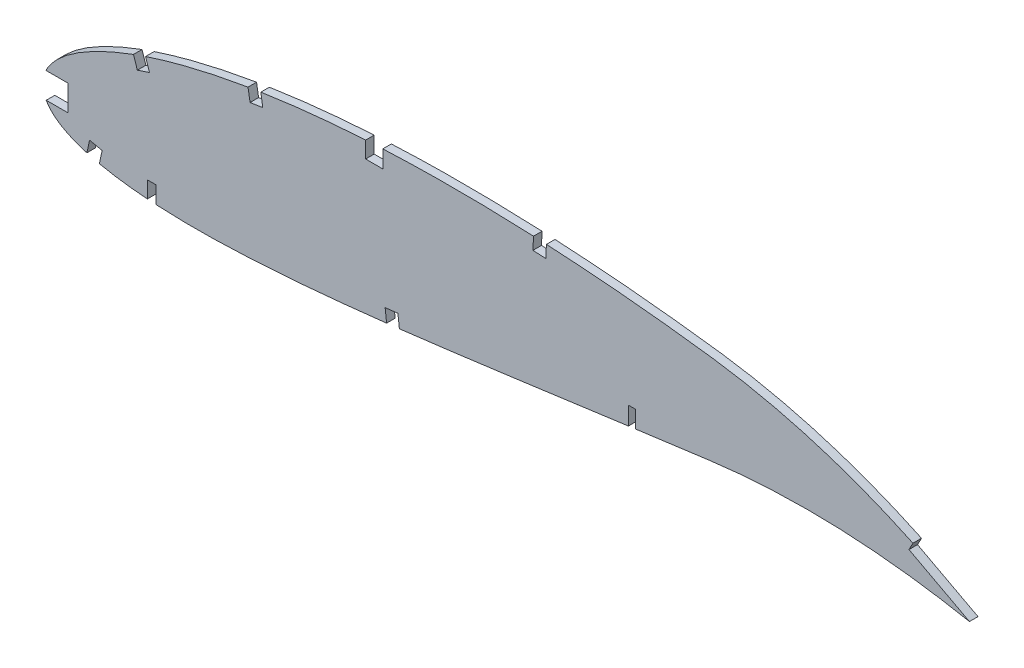
SolidWorks part; units mm, degrees
material "Plywood"
ref_plane "Front Plane" through (0, 0, 0) normal (0, 0, 1) x (1, 0, 0)
ref_plane "Top Plane" through (0, 0, 0) normal (0, 1, 0) x (1, 0, 0)
ref_plane "Right Plane" through (0, 0, 0) normal (1, 0, 0) x (0, 0, -1)
curve "Curve4"
  spline degree 3 poles (349.8746, 0.5455, 0) (349.8478, 0.562, 0) (349.7407, 0.6282, 0) (349.4993, 0.7762, 0) (349.0975, 1.0228, 0) (348.5349, 1.3661, 0) (347.8121, 1.8054, 0) (346.9286, 2.3375, 0) (345.885, 2.9606, 0) (344.6816, 3.6719, 0) (343.3185, 4.4681, 0) (341.7962, 5.3458, 0) (340.1148, 6.3001, 0) (338.275, 7.3272, 0) (336.2775, 8.422, 0) (334.1225, 9.5798, 0) (331.8109, 10.7946, 0) (329.3436, 12.0612, 0) (326.721, 13.3725, 0) (323.9443, 14.7232, 0) (321.0145, 16.1064, 0) (317.9326, 17.5149, 0) (314.7004, 18.9428, 0) (311.3186, 20.3813, 0) (307.7893, 21.8242, 0) (304.114, 23.2633, 0) (300.2949, 24.6919, 0) (296.3333, 26.1008, 0) (292.2323, 27.484, 0) (287.9939, 28.8323, 0) (283.6211, 30.1385, 0) (279.1164, 31.3942, 0) (274.4837, 32.5927, 0) (269.7257, 33.7256, 0) (264.8466, 34.785, 0) (259.8503, 35.7648, 0) (254.7409, 36.655, 0) (249.5326, 37.455, 0) (244.3091, 38.1205, 0) (239.0964, 38.7732, 0) (233.8915, 39.3864, 0) (228.623, 39.9736, 0) (223.2959, 40.5315, 0) (217.9156, 41.0583, 0) (212.4874, 41.5519, 0) (207.0171, 42.0107, 0) (201.5099, 42.4322, 0) (195.9716, 42.8157, 0) (190.4077, 43.1578, 0) (184.8241, 43.4583, 0) (179.2266, 43.7151, 0) (173.6208, 43.9264, 0) (168.0128, 44.0909, 0) (162.4085, 44.2071, 0) (156.8137, 44.2742, 0) (151.2345, 44.2904, 0) (145.6768, 44.2555, 0) (140.1465, 44.1681, 0) (134.6496, 44.0271, 0) (129.192, 43.8323, 0) (123.7796, 43.5837, 0) (118.4182, 43.2792, 0) (113.1138, 42.9209, 0) (107.8721, 42.5071, 0) (102.6991, 42.0378, 0) (97.6, 41.5149, 0) (92.5806, 40.937, 0) (87.6463, 40.3058, 0) (82.8024, 39.6225, 0) (78.0545, 38.8867, 0) (73.4074, 38.1005, 0) (68.8664, 37.2648, 0) (64.4362, 36.3819, 0) (60.1215, 35.4522, 0) (55.9271, 34.4784, 0) (51.8572, 33.4622, 0) (47.9162, 32.4055, 0) (44.1081, 31.3108, 0) (40.4368, 30.1806, 0) (36.9066, 29.0161, 0) (33.52, 27.8218, 0) (30.2813, 26.5985, 0) (27.193, 25.3499, 0) (24.2586, 24.0778, 0) (21.4804, 22.7861, 0) (18.8615, 21.4761, 0) (16.4038, 20.1517, 0) (14.1097, 18.8148, 0) (11.9815, 17.4679, 0) (10.02, 16.1143, 0) (8.2279, 14.7551, 0) (6.606, 13.3936, 0) (5.1551, 12.0318, 0) (3.8773, 10.6708, 0) (2.7727, 9.3129, 0) (1.8427, 7.9591, 0) (1.0874, 6.6108, 0) (0.5085, 5.269, 0) (0.1055, 3.9344, 0) (-0.1151, 2.6089, 0) (-0.17, 1.2916, 0) (-0.0566, 0.4299, 0) (0, 0, 0) knots 0 0 0 0 0.000254 0.001015 0.002283 0.004057 0.006331 0.009105 0.012374 0.016134 0.02038 0.025106 0.030306 0.035972 0.0421 0.048678 0.055702 0.06316 0.071046 0.07935 0.088063 0.097176 0.106678 0.116562 0.126814 0.137428 0.148394 0.1597 0.171338 0.183298 0.19557 0.208144 0.221012 0.234162 0.247587 0.261277 0.275223 0.289414 0.303771 0.317689 0.331784 0.34604 0.360444 0.374983 0.38964 0.404403 0.419257 0.434187 0.449177 0.464215 0.479284 0.49437 0.509458 0.524532 0.539579 0.554583 0.56953 0.584403 0.599191 0.613877 0.628447 0.642889 0.657186 0.671326 0.685294 0.699078 0.712665 0.726043 0.739198 0.752118 0.764792 0.777208 0.789356 0.801224 0.812804 0.824083 0.835055 0.84571 0.856038 0.866034 0.875689 0.884998 0.893953 0.902553 0.910789 0.918661 0.926166 0.933303 0.940071 0.946475 0.952518 0.958205 0.963547 0.968557 0.97325 0.977651 0.981787 0.985694 0.989415 0.993001 0.996508 1 1 1 1
curve "Curve5"
  spline degree 3 poles (0, 0, 0) (0.0898, -0.4241, 0) (0.27, -1.2744, 0) (0.7593, -2.4983, 0) (1.4064, -3.6749, 0) (2.2249, -4.801, 0) (3.2093, -5.8763, 0) (4.3574, -6.9018, 0) (5.6682, -7.8772, 0) (7.1398, -8.8018, 0) (8.7703, -9.6767, 0) (10.5577, -10.5014, 0) (12.5004, -11.2756, 0) (14.5962, -11.9982, 0) (16.8428, -12.6703, 0) (19.2378, -13.2904, 0) (21.7785, -13.8593, 0) (24.4626, -14.3755, 0) (27.2871, -14.8396, 0) (30.2491, -15.2513, 0) (33.3455, -15.6108, 0) (36.5732, -15.9174, 0) (39.9292, -16.1718, 0) (43.41, -16.3741, 0) (47.0123, -16.5249, 0) (50.7326, -16.6238, 0) (54.5673, -16.6722, 0) (58.5129, -16.6709, 0) (62.5656, -16.6195, 0) (66.7219, -16.5208, 0) (70.9777, -16.3742, 0) (75.3293, -16.1816, 0) (79.7728, -15.9448, 0) (84.3041, -15.6646, 0) (88.9192, -15.3423, 0) (93.6142, -14.9805, 0) (98.3848, -14.58, 0) (103.2269, -14.1432, 0) (108.136, -13.6724, 0) (113.1081, -13.1689, 0) (118.1387, -12.6351, 0) (123.2233, -12.0729, 0) (128.3576, -11.4851, 0) (133.537, -10.8728, 0) (138.7569, -10.2396, 0) (144.0126, -9.5866, 0) (149.2997, -8.9164, 0) (154.6133, -8.2321, 0) (159.9485, -7.5337, 0) (165.3008, -6.826, 0) (170.6651, -6.1086, 0) (176.0366, -5.3852, 0) (181.4105, -4.6578, 0) (186.7814, -3.9269, 0) (192.1447, -3.1954, 0) (197.4954, -2.4653, 0) (202.8282, -1.7368, 0) (208.1384, -1.0133, 0) (213.4205, -0.2949, 0) (218.6696, 0.417, 0) (223.8809, 1.1204, 0) (229.0493, 1.8142, 0) (234.1695, 2.4981, 0) (239.2364, 3.1723, 0) (244.169, 3.8163, 0) (248.9545, 4.4645, 0) (253.6088, 4.9959, 0) (258.2053, 5.4495, 0) (262.7485, 5.8213, 0) (267.2331, 6.1168, 0) (271.654, 6.3381, 0) (276.0058, 6.4882, 0) (280.283, 6.5716, 0) (284.4804, 6.5904, 0) (288.5922, 6.5507, 0) (292.613, 6.4555, 0) (296.5372, 6.3093, 0) (300.3594, 6.1169, 0) (304.0742, 5.8836, 0) (307.6759, 5.6128, 0) (311.1595, 5.3108, 0) (314.5196, 4.9821, 0) (317.7512, 4.6304, 0) (320.8494, 4.263, 0) (323.8094, 3.8825, 0) (326.6267, 3.4951, 0) (329.2966, 3.1046, 0) (331.8151, 2.7161, 0) (334.1781, 2.3332, 0) (336.3819, 1.9612, 0) (338.423, 1.6033, 0) (340.2977, 1.2632, 0) (342.0037, 0.9451, 0) (343.5374, 0.6506, 0) (344.8968, 0.3845, 0) (346.0794, 0.1481, 0) (347.0834, -0.0554, 0) (347.9072, -0.2251, 0) (348.5494, -0.3583, 0) (349.0088, -0.4551, 0) (349.2849, -0.5128, 0) (349.4076, -0.5389, 0) (349.4382, -0.5455, 0) knots 0 0 0 0 0.003638 0.007293 0.011028 0.014901 0.018963 0.023258 0.027821 0.032679 0.037853 0.043362 0.049215 0.055422 0.061989 0.068918 0.076211 0.083868 0.091887 0.100266 0.109 0.118085 0.127515 0.137285 0.147388 0.157816 0.168563 0.179619 0.190977 0.202627 0.21456 0.226767 0.239236 0.251959 0.264924 0.27812 0.291536 0.30516 0.318981 0.332985 0.347163 0.361499 0.375981 0.390597 0.405333 0.420175 0.43511 0.450124 0.465203 0.480333 0.495501 0.51069 0.525887 0.541078 0.556247 0.571382 0.586466 0.601485 0.616424 0.631269 0.646007 0.660621 0.675098 0.689423 0.703582 0.716908 0.730009 0.742952 0.755726 0.76832 0.780724 0.792927 0.804916 0.816679 0.828204 0.839475 0.850481 0.861208 0.871639 0.881763 0.891564 0.901027 0.910139 0.918884 0.927249 0.935221 0.942785 0.949928 0.956638 0.962904 0.968712 0.974054 0.978918 0.983297 0.98718 0.990561 0.993433 0.995791 0.99763 0.998946 0.999737 1 1 1 1
sketch "Sketch1" plane through (0, 0, 0) normal (0, 0, 1) x (1, 0, 0)
  line L24 (349.8746, 0.5455) -> (352.7074, -1.2046)
  line L25 (349.4382, -0.5455) -> (352.7074, -1.2046)
  spline S1 degree 3 poles (-6751.1592, -1841.0295) (107.2346, 81.5981) (-8.9881, 21.883) (0.7593, -2.4983) (1.4064, -3.6749) (2.2249, -4.801) (3.2093, -5.8763) (4.3574, -6.9018) (5.6682, -7.8772) (7.1398, -8.8018) (8.7703, -9.6767) (10.5577, -10.5014) (12.5004, -11.2756) (14.5962, -11.9982) (16.8428, -12.6703) (19.2378, -13.2904) (21.7785, -13.8593) (24.4626, -14.3755) (27.2871, -14.8396) (30.2491, -15.2513) (33.3455, -15.6108) (36.5732, -15.9174) (39.9292, -16.1718) (43.41, -16.3741) (47.0123, -16.5249) (50.7326, -16.6238) (54.5673, -16.6722) (58.5129, -16.6709) (62.5656, -16.6195) (66.7219, -16.5208) (70.9777, -16.3742) (75.3293, -16.1816) (79.7728, -15.9448) (84.3041, -15.6646) (88.9192, -15.3423) (93.6142, -14.9805) (98.3848, -14.58) (103.2269, -14.1432) (108.136, -13.6724) (113.1081, -13.1689) (118.1387, -12.6351) (123.2233, -12.0729) (128.3576, -11.4851) (133.537, -10.8728) (138.7569, -10.2396) (144.0126, -9.5866) (149.2997, -8.9164) (154.6133, -8.2321) (159.9485, -7.5337) (165.3008, -6.826) (170.6651, -6.1086) (176.0366, -5.3852) (181.4105, -4.6578) (186.7814, -3.9269) (192.1447, -3.1954) (197.4954, -2.4653) (202.8282, -1.7368) (208.1384, -1.0133) (213.4205, -0.2949) (218.6696, 0.417) (223.8809, 1.1204) (229.0493, 1.8142) (234.1695, 2.4981) (239.2364, 3.1723) (244.169, 3.8163) (248.9545, 4.4645) (253.6088, 4.9959) (258.2053, 5.4495) (262.7485, 5.8213) (267.2331, 6.1168) (271.654, 6.3381) (276.0058, 6.4882) (280.283, 6.5716) (284.4804, 6.5904) (288.5922, 6.5507) (292.613, 6.4555) (296.5372, 6.3093) (300.3594, 6.1169) (304.0742, 5.8836) (307.6759, 5.6128) (311.1595, 5.3108) (314.5196, 4.9821) (317.7512, 4.6304) (320.8494, 4.263) (323.8094, 3.8825) (326.6267, 3.4951) (329.2966, 3.1046) (331.8151, 2.7161) (334.1781, 2.3332) (336.3819, 1.9612) (338.423, 1.6033) (340.2977, 1.2632) (342.0037, 0.9451) (343.5374, 0.6506) (344.8968, 0.3845) (346.0794, 0.1481) (347.0834, -0.0554) (347.9072, -0.2251) (348.5494, -0.3583) (349.0088, -0.4551) (367.3245, -4.278) (382.9912, -19.8695) (1851.2191, 6833.2949) knots -0.208652 -0.208652 -0.208652 -0.208652 0.003638 0.007293 0.011028 0.014901 0.018963 0.023258 0.027821 0.032679 0.037853 0.043362 0.049215 0.055422 0.061989 0.068918 0.076211 0.083868 0.091887 0.100266 0.109 0.118085 0.127515 0.137285 0.147388 0.157816 0.168563 0.179619 0.190977 0.202627 0.21456 0.226767 0.239236 0.251959 0.264924 0.27812 0.291536 0.30516 0.318981 0.332985 0.347163 0.361499 0.375981 0.390597 0.405333 0.420175 0.43511 0.450124 0.465203 0.480333 0.495501 0.51069 0.525887 0.541078 0.556247 0.571382 0.586466 0.601485 0.616424 0.631269 0.646007 0.660621 0.675098 0.689423 0.703582 0.716908 0.730009 0.742952 0.755726 0.76832 0.780724 0.792927 0.804916 0.816679 0.828204 0.839475 0.850481 0.861208 0.871639 0.881763 0.891564 0.901027 0.910139 0.918884 0.927249 0.935221 0.942785 0.949928 0.956638 0.962904 0.968712 0.974054 0.978918 0.983297 0.98718 0.990561 0.993433 0.995791 0.99763 0.998946 0.999737 1.154885 1.154885 1.154885 1.154885 only from (0, 0) to (349.4382, -0.5455) construction
  spline S3 degree 3 poles (4072.2429, 5924.9131) (379.309, -30.208) (367.3101, -10.1487) (349.4993, 0.7762) (349.0975, 1.0228) (348.5349, 1.3661) (347.8121, 1.8054) (346.9286, 2.3375) (345.885, 2.9606) (344.6816, 3.6719) (343.3185, 4.4681) (341.7962, 5.3458) (340.1148, 6.3001) (338.275, 7.3272) (336.2775, 8.422) (334.1225, 9.5798) (331.8109, 10.7946) (329.3436, 12.0612) (326.721, 13.3725) (323.9443, 14.7232) (321.0145, 16.1064) (317.9326, 17.5149) (314.7004, 18.9428) (311.3186, 20.3813) (307.7893, 21.8242) (304.114, 23.2633) (300.2949, 24.6919) (296.3333, 26.1008) (292.2323, 27.484) (287.9939, 28.8323) (283.6211, 30.1385) (279.1164, 31.3942) (274.4837, 32.5927) (269.7257, 33.7256) (264.8466, 34.785) (259.8503, 35.7648) (254.7409, 36.655) (249.5326, 37.455) (244.3091, 38.1205) (239.0964, 38.7732) (233.8915, 39.3864) (228.623, 39.9736) (223.2959, 40.5315) (217.9156, 41.0583) (212.4874, 41.5519) (207.0171, 42.0107) (201.5099, 42.4322) (195.9716, 42.8157) (190.4077, 43.1578) (184.8241, 43.4583) (179.2266, 43.7151) (173.6208, 43.9264) (168.0128, 44.0909) (162.4085, 44.2071) (156.8137, 44.2742) (151.2345, 44.2904) (145.6768, 44.2555) (140.1465, 44.1681) (134.6496, 44.0271) (129.192, 43.8323) (123.7796, 43.5837) (118.4182, 43.2792) (113.1138, 42.9209) (107.8721, 42.5071) (102.6991, 42.0378) (97.6, 41.5149) (92.5806, 40.937) (87.6463, 40.3058) (82.8024, 39.6225) (78.0545, 38.8867) (73.4074, 38.1005) (68.8664, 37.2648) (64.4362, 36.3819) (60.1215, 35.4522) (55.9271, 34.4784) (51.8572, 33.4622) (47.9162, 32.4055) (44.1081, 31.3108) (40.4368, 30.1806) (36.9066, 29.0161) (33.52, 27.8218) (30.2813, 26.5985) (27.193, 25.3499) (24.2586, 24.0778) (21.4804, 22.7861) (18.8615, 21.4761) (16.4038, 20.1517) (14.1097, 18.8148) (11.9815, 17.4679) (10.02, 16.1143) (8.2279, 14.7551) (6.606, 13.3936) (5.1551, 12.0318) (3.8773, 10.6708) (2.7727, 9.3129) (1.8427, 7.9591) (1.0874, 6.6108) (0.5085, 5.269) (0.1055, 3.9344) (-0.1151, 2.6089) (-1.2068, -23.58) (128.5217, -41.162) (-6978.7548, -509.825) knots -0.166234 -0.166234 -0.166234 -0.166234 0.000254 0.001015 0.002283 0.004057 0.006331 0.009105 0.012374 0.016134 0.02038 0.025106 0.030306 0.035972 0.0421 0.048678 0.055702 0.06316 0.071046 0.07935 0.088063 0.097176 0.106678 0.116562 0.126814 0.137428 0.148394 0.1597 0.171338 0.183298 0.19557 0.208144 0.221012 0.234162 0.247587 0.261277 0.275223 0.289414 0.303771 0.317689 0.331784 0.34604 0.360444 0.374983 0.38964 0.404403 0.419257 0.434187 0.449177 0.464215 0.479284 0.49437 0.509458 0.524532 0.539579 0.554583 0.56953 0.584403 0.599191 0.613877 0.628447 0.642889 0.657186 0.671326 0.685294 0.699078 0.712665 0.726043 0.739198 0.752118 0.764792 0.777208 0.789356 0.801224 0.812804 0.824083 0.835055 0.84571 0.856038 0.866034 0.875689 0.884998 0.893953 0.902553 0.910789 0.918661 0.926166 0.933303 0.940071 0.946475 0.952518 0.958205 0.963547 0.968557 0.97325 0.977651 0.981787 0.985694 0.989415 0.993001 0.996508 1.199844 1.199844 1.199844 1.199844 only from (349.8746, 0.5455) to (0, 0) construction
  spline S4 degree 3 poles (0, 0) (0.0898, -0.4241) (0.27, -1.2744) (0.7593, -2.4983) (1.4064, -3.6749) (2.2249, -4.801) (3.2093, -5.8763) (4.3574, -6.9018) (5.6682, -7.8772) (7.1398, -8.8018) (8.7703, -9.6767) (10.5577, -10.5014) (12.5004, -11.2756) (14.5962, -11.9982) (16.8428, -12.6703) (19.2378, -13.2904) (21.7785, -13.8593) (24.4626, -14.3755) (27.2871, -14.8396) (30.2491, -15.2513) (33.3455, -15.6108) (36.5732, -15.9174) (39.9292, -16.1718) (43.41, -16.3741) (47.0123, -16.5249) (50.7326, -16.6238) (54.5673, -16.6722) (58.5129, -16.6709) (62.5656, -16.6195) (66.7219, -16.5208) (70.9777, -16.3742) (75.3293, -16.1816) (79.7728, -15.9448) (84.3041, -15.6646) (88.9192, -15.3423) (93.6142, -14.9805) (98.3848, -14.58) (103.2269, -14.1432) (108.136, -13.6724) (113.1081, -13.1689) (118.1387, -12.6351) (123.2233, -12.0729) (128.3576, -11.4851) (133.537, -10.8728) (138.7569, -10.2396) (144.0126, -9.5866) (149.2997, -8.9164) (154.6133, -8.2321) (159.9485, -7.5337) (165.3008, -6.826) (170.6651, -6.1086) (176.0366, -5.3852) (181.4105, -4.6578) (186.7814, -3.9269) (192.1447, -3.1954) (197.4954, -2.4653) (202.8282, -1.7368) (208.1384, -1.0133) (213.4205, -0.2949) (218.6696, 0.417) (223.8809, 1.1204) (229.0493, 1.8142) (234.1695, 2.4981) (239.2364, 3.1723) (244.169, 3.8163) (248.9545, 4.4645) (253.6088, 4.9959) (258.2053, 5.4495) (262.7485, 5.8213) (267.2331, 6.1168) (271.654, 6.3381) (276.0058, 6.4882) (280.283, 6.5716) (284.4804, 6.5904) (288.5922, 6.5507) (292.613, 6.4555) (296.5372, 6.3093) (300.3594, 6.1169) (304.0742, 5.8836) (307.6759, 5.6128) (311.1595, 5.3108) (314.5196, 4.9821) (317.7512, 4.6304) (320.8494, 4.263) (323.8094, 3.8825) (326.6267, 3.4951) (329.2966, 3.1046) (331.8151, 2.7161) (334.1781, 2.3332) (336.3819, 1.9612) (338.423, 1.6033) (340.2977, 1.2632) (342.0037, 0.9451) (343.5374, 0.6506) (344.8968, 0.3845) (346.0794, 0.1481) (347.0834, -0.0554) (347.9072, -0.2251) (348.5494, -0.3583) (349.0088, -0.4551) (349.2849, -0.5128) (349.4076, -0.5389) (349.4382, -0.5455) knots 0 0 0 0 0.003638 0.007293 0.011028 0.014901 0.018963 0.023258 0.027821 0.032679 0.037853 0.043362 0.049215 0.055422 0.061989 0.068918 0.076211 0.083868 0.091887 0.100266 0.109 0.118085 0.127515 0.137285 0.147388 0.157816 0.168563 0.179619 0.190977 0.202627 0.21456 0.226767 0.239236 0.251959 0.264924 0.27812 0.291536 0.30516 0.318981 0.332985 0.347163 0.361499 0.375981 0.390597 0.405333 0.420175 0.43511 0.450124 0.465203 0.480333 0.495501 0.51069 0.525887 0.541078 0.556247 0.571382 0.586466 0.601485 0.616424 0.631269 0.646007 0.660621 0.675098 0.689423 0.703582 0.716908 0.730009 0.742952 0.755726 0.76832 0.780724 0.792927 0.804916 0.816679 0.828204 0.839475 0.850481 0.861208 0.871639 0.881763 0.891564 0.901027 0.910139 0.918884 0.927249 0.935221 0.942785 0.949928 0.956638 0.962904 0.968712 0.974054 0.978918 0.983297 0.98718 0.990561 0.993433 0.995791 0.99763 0.998946 0.999737 1 1 1 1
  spline S5 degree 3 poles (349.8746, 0.5455) (349.8478, 0.562) (349.7407, 0.6282) (349.4993, 0.7762) (349.0975, 1.0228) (348.5349, 1.3661) (347.8121, 1.8054) (346.9286, 2.3375) (345.885, 2.9606) (344.6816, 3.6719) (343.3185, 4.4681) (341.7962, 5.3458) (340.1148, 6.3001) (338.275, 7.3272) (336.2775, 8.422) (334.1225, 9.5798) (331.8109, 10.7946) (329.3436, 12.0612) (326.721, 13.3725) (323.9443, 14.7232) (321.0145, 16.1064) (317.9326, 17.5149) (314.7004, 18.9428) (311.3186, 20.3813) (307.7893, 21.8242) (304.114, 23.2633) (300.2949, 24.6919) (296.3333, 26.1008) (292.2323, 27.484) (287.9939, 28.8323) (283.6211, 30.1385) (279.1164, 31.3942) (274.4837, 32.5927) (269.7257, 33.7256) (264.8466, 34.785) (259.8503, 35.7648) (254.7409, 36.655) (249.5326, 37.455) (244.3091, 38.1205) (239.0964, 38.7732) (233.8915, 39.3864) (228.623, 39.9736) (223.2959, 40.5315) (217.9156, 41.0583) (212.4874, 41.5519) (207.0171, 42.0107) (201.5099, 42.4322) (195.9716, 42.8157) (190.4077, 43.1578) (184.8241, 43.4583) (179.2266, 43.7151) (173.6208, 43.9264) (168.0128, 44.0909) (162.4085, 44.2071) (156.8137, 44.2742) (151.2345, 44.2904) (145.6768, 44.2555) (140.1465, 44.1681) (134.6496, 44.0271) (129.192, 43.8323) (123.7796, 43.5837) (118.4182, 43.2792) (113.1138, 42.9209) (107.8721, 42.5071) (102.6991, 42.0378) (97.6, 41.5149) (92.5806, 40.937) (87.6463, 40.3058) (82.8024, 39.6225) (78.0545, 38.8867) (73.4074, 38.1005) (68.8664, 37.2648) (64.4362, 36.3819) (60.1215, 35.4522) (55.9271, 34.4784) (51.8572, 33.4622) (47.9162, 32.4055) (44.1081, 31.3108) (40.4368, 30.1806) (36.9066, 29.0161) (33.52, 27.8218) (30.2813, 26.5985) (27.193, 25.3499) (24.2586, 24.0778) (21.4804, 22.7861) (18.8615, 21.4761) (16.4038, 20.1517) (14.1097, 18.8148) (11.9815, 17.4679) (10.02, 16.1143) (8.2279, 14.7551) (6.606, 13.3936) (5.1551, 12.0318) (3.8773, 10.6708) (2.7727, 9.3129) (1.8427, 7.9591) (1.0874, 6.6108) (0.5085, 5.269) (0.1055, 3.9344) (-0.1151, 2.6089) (-0.17, 1.2916) (-0.0566, 0.4299) (0, 0) knots 0 0 0 0 0.000254 0.001015 0.002283 0.004057 0.006331 0.009105 0.012374 0.016134 0.02038 0.025106 0.030306 0.035972 0.0421 0.048678 0.055702 0.06316 0.071046 0.07935 0.088063 0.097176 0.106678 0.116562 0.126814 0.137428 0.148394 0.1597 0.171338 0.183298 0.19557 0.208144 0.221012 0.234162 0.247587 0.261277 0.275223 0.289414 0.303771 0.317689 0.331784 0.34604 0.360444 0.374983 0.38964 0.404403 0.419257 0.434187 0.449177 0.464215 0.479284 0.49437 0.509458 0.524532 0.539579 0.554583 0.56953 0.584403 0.599191 0.613877 0.628447 0.642889 0.657186 0.671326 0.685294 0.699078 0.712665 0.726043 0.739198 0.752118 0.764792 0.777208 0.789356 0.801224 0.812804 0.824083 0.835055 0.84571 0.856038 0.866034 0.875689 0.884998 0.893953 0.902553 0.910789 0.918661 0.926166 0.933303 0.940071 0.946475 0.952518 0.958205 0.963547 0.968557 0.97325 0.977651 0.981787 0.985694 0.989415 0.993001 0.996508 1 1 1 1
extrude "Boss-Extrude1" add sketch "Sketch1" along normal blind 3.175
sketch "Sketch2" plane through (0, 0, 0) normal (0, 0, -1) x (-1, 0, 0)
  line L0 (-219.6066, 6.9148) -> (-217.0666, 6.9148)
  line L1 (-219.6066, 0.5647) -> (-219.6066, 6.9148)
  line L2 (-217.0666, 0.5647) -> (-217.0666, -0.7899)
  line L3 (-125.9441, 43.5934) -> (-125.9441, 37.241)
  line L4 (-217.0666, -0.7899) -> (-219.6066, -0.1126)
  line L5 (-41.8066, -16.2784) -> (-41.8066, -9.9284)
  line L6 (-219.6066, -0.1126) -> (-219.6066, 0.5647)
  line L7 (-38.6316, -16.2784) -> (-38.6316, -9.9284)
  line L8 (-125.9441, 37.241) -> (-119.5941, 37.241)
  line L9 (-119.5941, 43.5934) -> (-119.5941, 37.241)
  line L10 (-125.9441, 43.5934) -> (-125.9441, 46.4957)
  line L11 (-217.0666, 0.5647) -> (-217.0666, 6.9148)
  line L12 (-125.9441, 46.4957) -> (-119.5941, 44.8024)
  line L13 (-119.5941, 44.8024) -> (-119.5941, 43.5934)
  line L14 (-41.8066, -16.2784) -> (-38.6316, -16.2784)
  line L15 (-41.8066, -9.9284) -> (-38.6316, -9.9284)
extrude "Cut-Extrude1" cut sketch "Sketch2" against normal blind 7.62
sketch "Sketch3" plane through (0, 0, 3.175) normal (0, 0, 1) x (1, 0, 0)
  line L1 (-0.4071, 6.4083) -> (9.1179, 6.4083)
  line L2 (16.1715, -12.5452) -> (15.7059, -14.4019)
  line L3 (9.1179, -3.1167) -> (9.1179, 6.4083)
  line L4 (20.793, -13.704) -> (20.3275, -15.5607)
  line L5 (39.4213, 24.9477) -> (37.9149, 29.4655)
  line L6 (15.7059, -14.4019) -> (20.3275, -15.5607)
  line L7 (20.793, -13.704) -> (21.8392, -8.9067)
  line L9 (21.8392, -8.9067) -> (17.1861, -7.8921)
  line L10 (127.3683, -11.6175) -> (127.6344, -13.8855)
  line L11 (81.4236, 34.6803) -> (80.6994, 39.3875)
  line L12 (132.1136, -11.0609) -> (132.3796, -13.3289)
  line L13 (132.1136, -11.0609) -> (131.5505, -6.3243)
  line L14 (127.6344, -13.8855) -> (132.3796, -13.3289)
  line L15 (131.5505, -6.3243) -> (126.8213, -6.8865)
  line L17 (186.4034, 38.6915) -> (186.6522, 43.4474)
  line L19 (-0.4071, -3.1167) -> (-0.4071, 6.4083)
  line L21 (-0.4071, -3.1167) -> (9.1179, -3.1167)
  line L23 (33.4172, 27.8983) -> (34.9034, 23.4412)
  line L25 (34.9034, 23.4412) -> (39.4213, 24.9477)
  line L27 (17.1861, -7.8921) -> (16.1715, -12.5452)
  line L29 (75.932, 38.6201) -> (76.7164, 33.9561)
  line L31 (76.7164, 33.9561) -> (81.4236, 34.6803)
  line L33 (126.8213, -6.8865) -> (127.3683, -11.6175)
  line L35 (181.8631, 43.6817) -> (181.6474, 38.9402)
  line L37 (181.6474, 38.9402) -> (186.4034, 38.6915)
  arc A1 (186.6522, 43.4474) -> (181.8631, 43.6817) centre (149.7221, -662.3427) ccw
  spline S1 degree 3 poles (37.9149, 29.4655) (37.5031, 29.3282) (35.9987, 28.8207) (34.5011, 28.2932) (33.4172, 27.8983) knots 0 0 0 0 0.273428 1 1 1 1
  spline S3 degree 3 poles (80.6994, 39.3875) (79.7758, 39.2454) (78.1859, 38.9943) (76.5977, 38.7321) (75.932, 38.6201) knots 0 0 0 0 0.580571 1 1 1 1
extrude "Cut-Extrude2" cut sketch "Sketch3" against normal blind 7.62
sketch "Sketch4" plane through (0, 0, 3.175) normal (0, 0, 1) x (1, 0, 0)
  line L0 (322.6191, 15.347) -> (321.1318, 12.542)
  line L1 (322.6191, 15.347) -> (345.0596, 3.448)
  line L2 (321.1318, 12.542) -> (343.5722, 0.6429)
  line L3 (345.0596, 3.448) -> (343.5722, 0.6429)
  line L29 (1.0177, 6.4083) -> (9.1179, 6.4083)
  line L30 (9.1179, 6.4083) -> (9.1179, -3.1167)
  line L31 (9.1179, -3.1167) -> (1.1073, -3.1167)
  line L32 (16.1882, -12.4685) -> (17.1861, -7.8921)
  line L33 (17.1861, -7.8921) -> (21.8392, -8.9067)
  line L34 (21.8392, -8.9067) -> (20.8074, -13.6378)
  line L35 (38.6316, -16.0704) -> (38.6316, -9.9284)
  line L36 (38.6316, -9.9284) -> (41.8066, -9.9284)
  line L37 (41.8066, -9.9284) -> (41.8066, -16.2784)
  line L38 (127.366, -11.5969) -> (126.8213, -6.8865)
  line L39 (126.8213, -6.8865) -> (131.5505, -6.3243)
  line L40 (131.5505, -6.3243) -> (132.1111, -11.0403)
  line L41 (217.0666, 0.1994) -> (217.0666, 6.9148)
  line L42 (217.0666, 6.9148) -> (219.6066, 6.9148)
  line L43 (219.6066, 6.9148) -> (219.6066, 0.5432)
  line L44 (349.4382, -0.5455) -> (352.7074, -1.2046)
  line L45 (352.7074, -1.2046) -> (349.8746, 0.5455)
  line L46 (186.6475, 43.3577) -> (186.4034, 38.6915)
  line L47 (186.4034, 38.6915) -> (181.6474, 38.9402)
  line L48 (181.6474, 38.9402) -> (181.8591, 43.5924)
  line L49 (125.9441, 43.6804) -> (125.9441, 37.241)
  line L50 (125.9441, 37.241) -> (119.5941, 37.241)
  line L51 (119.5941, 37.241) -> (119.5941, 43.3413)
  line L52 (80.7135, 39.2958) -> (81.4236, 34.6803)
  line L53 (81.4236, 34.6803) -> (76.7164, 33.9561)
  line L54 (76.7164, 33.9561) -> (75.9476, 38.5273)
  line L55 (37.9515, 29.3559) -> (39.4213, 24.9477)
  line L56 (39.4213, 24.9477) -> (34.9034, 23.4412)
  line L57 (34.9034, 23.4412) -> (33.4552, 27.7843)
  line L58 (1.0177, 6.4083) -> (9.1179, 6.4083)
  line L59 (9.1179, 6.4083) -> (9.1179, -3.1167)
  line L60 (9.1179, -3.1167) -> (1.1073, -3.1167)
  line L61 (16.1882, -12.4685) -> (17.1861, -7.8921)
  line L62 (17.1861, -7.8921) -> (21.8392, -8.9067)
  line L63 (21.8392, -8.9067) -> (20.8074, -13.6378)
  line L64 (38.6316, -16.0704) -> (38.6316, -9.9284)
  line L65 (38.6316, -9.9284) -> (41.8066, -9.9284)
  line L66 (41.8066, -9.9284) -> (41.8066, -16.2784)
  line L67 (127.366, -11.5969) -> (126.8213, -6.8865)
  line L68 (126.8213, -6.8865) -> (131.5505, -6.3243)
  line L69 (131.5505, -6.3243) -> (132.1111, -11.0403)
  line L70 (217.0666, 0.1994) -> (217.0666, 6.9148)
  line L71 (217.0666, 6.9148) -> (219.6066, 6.9148)
  line L72 (219.6066, 6.9148) -> (219.6066, 0.5432)
  line L73 (349.4382, -0.5455) -> (352.7074, -1.2046)
  line L74 (352.7074, -1.2046) -> (349.8746, 0.5455)
  line L75 (186.6475, 43.3577) -> (186.4034, 38.6915)
  line L76 (186.4034, 38.6915) -> (181.6474, 38.9402)
  line L77 (181.6474, 38.9402) -> (181.8591, 43.5924)
  line L78 (125.9441, 43.6804) -> (125.9441, 37.241)
  line L79 (125.9441, 37.241) -> (119.5941, 37.241)
  line L80 (119.5941, 37.241) -> (119.5941, 43.3413)
  line L81 (80.7135, 39.2958) -> (81.4236, 34.6803)
  line L82 (81.4236, 34.6803) -> (76.7164, 33.9561)
  line L83 (76.7164, 33.9561) -> (75.9476, 38.5273)
  line L84 (37.9515, 29.3559) -> (39.4213, 24.9477)
  line L85 (39.4213, 24.9477) -> (34.9034, 23.4412)
  line L86 (34.9034, 23.4412) -> (33.4552, 27.7843)
  spline S10 degree 3 poles (-2134.0221, 3364.7605) (538.8254, -195.9198) (211.3259, 99.792) (27.193, 25.3499) (24.2586, 24.0778) (21.4804, 22.7861) (18.8615, 21.4761) (16.4038, 20.1517) (14.1097, 18.8148) (11.9815, 17.4679) (10.02, 16.1143) (8.2279, 14.7551) (6.606, 13.3936) (5.1551, 12.0318) (3.8773, 10.6708) (2.7727, 9.3129) (1.8427, 7.9591) (-20.1055, -31.2195) (140.4638, -160.6153) (3982.6931, 317.4313) knots -0.699136 -0.699136 -0.699136 -0.699136 0.884998 0.893953 0.902553 0.910789 0.918661 0.926166 0.933303 0.940071 0.946475 0.952518 0.958205 0.963547 0.968557 0.97325 0.977651 0.981787 1.334861 1.334861 1.334861 1.334861 only from (33.4552, 27.7843) to (1.0177, 6.4083)
  spline S11 degree 3 poles (2938.0839, -2689.8405) (246.7778, 269.8068) (-28.0545, 36.8583) (2.2249, -4.801) (3.2093, -5.8763) (4.3574, -6.9018) (5.6682, -7.8772) (7.1398, -8.8018) (8.7703, -9.6767) (10.5577, -10.5014) (12.5004, -11.2756) (106.4904, -43.6815) (280.4844, 176.1899) (-1938.6252, -3496.6913) knots -0.412769 -0.412769 -0.412769 -0.412769 0.011028 0.014901 0.018963 0.023258 0.027821 0.032679 0.037853 0.043362 0.049215 0.055422 0.878689 0.878689 0.878689 0.878689 only from (1.1073, -3.1167) to (16.1882, -12.4685)
  spline S12 degree 3 poles (1320.3281, 3756.9994) (-146.0598, 213.5353) (-80.6979, 5.8491) (24.4626, -14.3755) (27.2871, -14.8396) (30.2491, -15.2513) (33.3455, -15.6108) (213.0584, -32.6822) (415.285, 227.9801) (-474.0394, -3957.3928) knots -0.808032 -0.808032 -0.808032 -0.808032 0.076211 0.083868 0.091887 0.100266 0.109 0.118085 1.617405 1.617405 1.617405 1.617405 only from (20.8074, -13.6378) to (38.6316, -16.0704)
  spline S13 degree 3 poles (256.2221, 3952.659) (-280.3063, 190.6076) (-122.0561, -9.444) (47.0123, -16.5249) (50.7326, -16.6238) (54.5673, -16.6722) (58.5129, -16.6709) (62.5656, -16.6195) (66.7219, -16.5208) (70.9777, -16.3742) (75.3293, -16.1816) (79.7728, -15.9448) (84.3041, -15.6646) (88.9192, -15.3423) (93.6142, -14.9805) (98.3848, -14.58) (103.2269, -14.1432) (108.136, -13.6724) (113.1081, -13.1689) (118.1387, -12.6351) (616.9364, 42.523) (1082.5995, 376.7415) (1720.9864, -3408.5986) knots -1.264346 -1.264346 -1.264346 -1.264346 0.137285 0.147388 0.157816 0.168563 0.179619 0.190977 0.202627 0.21456 0.226767 0.239236 0.251959 0.264924 0.27812 0.291536 0.30516 0.318981 0.332985 0.347163 0.361499 4.550792 4.550792 4.550792 4.550792 only from (41.8066, -16.2784) to (127.366, -11.5969)
  spline S14 degree 3 poles (-1205.6276, 3667.8196) (-512.3075, 1.844) (-182.27, -49.1822) (138.7569, -10.2396) (144.0126, -9.5866) (149.2997, -8.9164) (154.6133, -8.2321) (159.9485, -7.5337) (165.3008, -6.826) (170.6651, -6.1086) (176.0366, -5.3852) (181.4105, -4.6578) (186.7814, -3.9269) (192.1447, -3.1954) (197.4954, -2.4653) (202.8282, -1.7368) (208.1384, -1.0133) (637.4453, 57.377) (1067.6455, 95.9352) (1973.8247, -3421.787) knots -2.297748 -2.297748 -2.297748 -2.297748 0.390597 0.405333 0.420175 0.43511 0.450124 0.465203 0.480333 0.495501 0.51069 0.525887 0.541078 0.556247 0.571382 0.586466 0.601485 0.616424 4.2279 4.2279 4.2279 4.2279 only from (132.1111, -11.0403) to (217.0666, 0.1994)
  spline S15 degree 3 poles (-2257.0625, 2699.4045) (-1158.0495, -286.0267) (-472.0862, -92.3082) (229.0493, 1.8142) (234.1695, 2.4981) (239.2364, 3.1723) (244.169, 3.8163) (248.9545, 4.4645) (253.6088, 4.9959) (258.2053, 5.4495) (262.7485, 5.8213) (267.2331, 6.1168) (271.654, 6.3381) (276.0058, 6.4882) (280.283, 6.5716) (284.4804, 6.5904) (288.5922, 6.5507) (292.613, 6.4555) (296.5372, 6.3093) (300.3594, 6.1169) (304.0742, 5.8836) (307.6759, 5.6128) (311.1595, 5.3108) (314.5196, 4.9821) (317.7512, 4.6304) (320.8494, 4.263) (323.8094, 3.8825) (326.6267, 3.4951) (329.2966, 3.1046) (331.8151, 2.7161) (334.1781, 2.3332) (336.3819, 1.9612) (338.423, 1.6033) (340.2977, 1.2632) (342.0037, 0.9451) (343.5374, 0.6506) (344.8968, 0.3845) (346.0794, 0.1481) (347.0834, -0.0554) (347.9072, -0.2251) (348.5494, -0.3583) (349.0088, -0.4551) (364.249, -3.6361) (377.6138, -14.9276) (1220.6198, 3897.1166) knots -5.270622 -5.270622 -5.270622 -5.270622 0.646007 0.660621 0.675098 0.689423 0.703582 0.716908 0.730009 0.742952 0.755726 0.76832 0.780724 0.792927 0.804916 0.816679 0.828204 0.839475 0.850481 0.861208 0.871639 0.881763 0.891564 0.901027 0.910139 0.918884 0.927249 0.935221 0.942785 0.949928 0.956638 0.962904 0.968712 0.974054 0.978918 0.983297 0.98718 0.990561 0.993433 0.995791 0.99763 0.998946 0.999737 1.128479 1.128479 1.128479 1.128479 only from (219.6066, 0.5432) to (349.4382, -0.5455)
  spline S16 degree 3 poles (2490.5398, 3377.5083) (375.0876, -23.686) (364.3203, -8.3148) (349.4993, 0.7762) (349.0975, 1.0228) (348.5349, 1.3661) (347.8121, 1.8054) (346.9286, 2.3375) (345.885, 2.9606) (344.6816, 3.6719) (343.3185, 4.4681) (341.7962, 5.3458) (340.1148, 6.3001) (338.275, 7.3272) (336.2775, 8.422) (334.1225, 9.5798) (331.8109, 10.7946) (329.3436, 12.0612) (326.721, 13.3725) (323.9443, 14.7232) (321.0145, 16.1064) (317.9326, 17.5149) (314.7004, 18.9428) (311.3186, 20.3813) (307.7893, 21.8242) (304.114, 23.2633) (300.2949, 24.6919) (296.3333, 26.1008) (292.2323, 27.484) (287.9939, 28.8323) (283.6211, 30.1385) (279.1164, 31.3942) (274.4837, 32.5927) (269.7257, 33.7256) (264.8466, 34.785) (259.8503, 35.7648) (254.7409, 36.655) (249.5326, 37.455) (244.3091, 38.1205) (239.0964, 38.7732) (233.8915, 39.3864) (228.623, 39.9736) (223.2959, 40.5315) (217.9156, 41.0583) (212.4874, 41.5519) (207.0171, 42.0107) (201.5099, 42.4322) (195.9716, 42.8157) (-225.3258, 68.7211) (-665.6508, -267.5515) (-642.8416, -3720.9143) knots -0.137946 -0.137946 -0.137946 -0.137946 0.000254 0.001015 0.002283 0.004057 0.006331 0.009105 0.012374 0.016134 0.02038 0.025106 0.030306 0.035972 0.0421 0.048678 0.055702 0.06316 0.071046 0.07935 0.088063 0.097176 0.106678 0.116562 0.126814 0.137428 0.148394 0.1597 0.171338 0.183298 0.19557 0.208144 0.221012 0.234162 0.247587 0.261277 0.275223 0.289414 0.303771 0.317689 0.331784 0.34604 0.360444 0.374983 0.38964 0.404403 0.419257 0.434187 0.449177 3.823488 3.823488 3.823488 3.823488 only from (349.8746, 0.5455) to (186.6475, 43.3577)
  spline S17 degree 3 poles (397.9971, 3747.2003) (1269.2038, -686.9297) (736.7491, 22.7012) (173.6208, 43.9264) (168.0128, 44.0909) (162.4085, 44.2071) (156.8137, 44.2742) (151.2345, 44.2904) (145.6768, 44.2555) (140.1465, 44.1681) (134.6496, 44.0271) (-175.9031, 32.9409) (-473.7116, -246.5926) (-120.8661, -3868.3573) knots -4.035458 -4.035458 -4.035458 -4.035458 0.479284 0.49437 0.509458 0.524532 0.539579 0.554583 0.56953 0.584403 0.599191 0.613877 3.090627 3.090627 3.090627 3.090627 only from (181.8591, 43.5924) to (125.9441, 43.6804)
  spline S18 degree 3 poles (-1611.9531, -2955.2756) (1354.7481, -919.9884) (702.4277, 82.7342) (113.1138, 42.9209) (107.8721, 42.5071) (102.6991, 42.0378) (97.6, 41.5149) (92.5806, 40.937) (87.6463, 40.3058) (-218.3261, -2.8582) (-464.5142, -438.9889) (803.447, -3803.0856) knots -4.092349 -4.092349 -4.092349 -4.092349 0.642889 0.657186 0.671326 0.685294 0.699078 0.712665 0.726043 0.739198 3.204755 3.204755 3.204755 3.204755 only from (119.5941, 43.3413) to (80.7135, 39.2958)
  spline S19 degree 3 poles (-862.5367, 3849.435) (767.3987, -298.6203) (379.1826, 94.3752) (68.8664, 37.2648) (64.4362, 36.3819) (60.1215, 35.4522) (55.9271, 34.4784) (51.8572, 33.4622) (47.9162, 32.4055) (44.1081, 31.3108) (-149.9138, -28.4186) (-244.8123, -394.9512) (1700.1754, -3563.2159) knots -1.75535 -1.75535 -1.75535 -1.75535 0.764792 0.777208 0.789356 0.801224 0.812804 0.824083 0.835055 0.84571 0.856038 2.47225 2.47225 2.47225 2.47225 only from (75.9476, 38.5273) to (37.9515, 29.3559)
  spline S20 degree 3 poles (33.4552, 27.7843) (32.3808, 27.3915) (30.2718, 26.5946) (27.193, 25.3499) (24.2586, 24.0778) (21.4804, 22.7861) (18.8615, 21.4761) (16.4038, 20.1517) (14.1097, 18.8148) (11.9815, 17.4679) (10.02, 16.1143) (8.2279, 14.7551) (6.606, 13.3936) (5.1551, 12.0318) (3.8773, 10.6708) (2.7727, 9.3129) (1.8427, 7.9591) (1.2945, 6.9806) (1.0441, 6.4637) (1.0177, 6.4083) knots 0.875772 0.875772 0.875772 0.875772 0.884998 0.893953 0.902553 0.910789 0.918661 0.926166 0.933303 0.940071 0.946475 0.952518 0.958205 0.963547 0.968557 0.97325 0.977651 0.981787 0.982281 0.982281 0.982281 0.982281
  spline S21 degree 3 poles (1.1073, -3.1167) (1.2071, -3.296) (1.5474, -3.8689) (2.2249, -4.801) (3.2093, -5.8763) (4.3574, -6.9018) (5.6682, -7.8772) (7.1398, -8.8018) (8.7703, -9.6767) (10.5577, -10.5014) (12.5004, -11.2756) (14.394, -11.9284) (15.6433, -12.3102) (16.1882, -12.4685) knots 0.009304 0.009304 0.009304 0.009304 0.011028 0.014901 0.018963 0.023258 0.027821 0.032679 0.037853 0.043362 0.049215 0.055422 0.060192 0.060192 0.060192 0.060192
  spline S22 degree 3 poles (20.8074, -13.6378) (21.1175, -13.706) (22.3189, -13.9632) (24.4626, -14.3755) (27.2871, -14.8396) (30.2491, -15.2513) (33.3455, -15.6108) (36.1547, -15.8776) (37.9318, -16.0188) (38.6316, -16.0704) knots 0.073543 0.073543 0.073543 0.073543 0.076211 0.083868 0.091887 0.100266 0.109 0.118085 0.123982 0.123982 0.123982 0.123982
  spline S23 degree 3 poles (41.8066, -16.2784) (42.3279, -16.3084) (44.0497, -16.4009) (47.0123, -16.5249) (50.7326, -16.6238) (54.5673, -16.6722) (58.5129, -16.6709) (62.5656, -16.6195) (66.7219, -16.5208) (70.9777, -16.3742) (75.3293, -16.1816) (79.7728, -15.9448) (84.3041, -15.6646) (88.9192, -15.3423) (93.6142, -14.9805) (98.3848, -14.58) (103.2269, -14.1432) (108.136, -13.6724) (113.1081, -13.1689) (118.1387, -12.6351) (122.898, -12.1088) (125.9794, -11.7572) (127.366, -11.5969) knots 0.132896 0.132896 0.132896 0.132896 0.137285 0.147388 0.157816 0.168563 0.179619 0.190977 0.202627 0.21456 0.226767 0.239236 0.251959 0.264924 0.27812 0.291536 0.30516 0.318981 0.332985 0.347163 0.361499 0.37323 0.37323 0.37323 0.37323
  spline S24 degree 3 poles (132.1111, -11.0403) (132.5816, -10.9844) (134.793, -10.7205) (138.7569, -10.2396) (144.0126, -9.5866) (149.2997, -8.9164) (154.6133, -8.2321) (159.9485, -7.5337) (165.3008, -6.826) (170.6651, -6.1086) (176.0366, -5.3852) (181.4105, -4.6578) (186.7814, -3.9269) (192.1447, -3.1954) (197.4954, -2.4653) (202.8282, -1.7368) (208.1384, -1.0133) (212.8819, -0.3682) (215.8549, 0.0352) (217.0666, 0.1994) knots 0.386615 0.386615 0.386615 0.386615 0.390597 0.405333 0.420175 0.43511 0.450124 0.465203 0.480333 0.495501 0.51069 0.525887 0.541078 0.556247 0.571382 0.586466 0.601485 0.616424 0.626701 0.626701 0.626701 0.626701
  spline S25 degree 3 poles (219.6066, 0.5432) (221.0361, 0.7364) (224.189, 1.1617) (229.0493, 1.8142) (234.1695, 2.4981) (239.2364, 3.1723) (244.169, 3.8163) (248.9545, 4.4645) (253.6088, 4.9959) (258.2053, 5.4495) (262.7485, 5.8213) (267.2331, 6.1168) (271.654, 6.3381) (276.0058, 6.4882) (280.283, 6.5716) (284.4804, 6.5904) (288.5922, 6.5507) (292.613, 6.4555) (296.5372, 6.3093) (300.3594, 6.1169) (304.0742, 5.8836) (307.6759, 5.6128) (311.1595, 5.3108) (314.5196, 4.9821) (317.7512, 4.6304) (320.8494, 4.263) (323.8094, 3.8825) (326.6267, 3.4951) (329.2966, 3.1046) (331.8151, 2.7161) (334.1781, 2.3332) (336.3819, 1.9612) (338.423, 1.6033) (340.2977, 1.2632) (342.0037, 0.9451) (343.5374, 0.6506) (344.8968, 0.3845) (346.0794, 0.1481) (347.0834, -0.0554) (347.9072, -0.2251) (348.5494, -0.3583) (349.0088, -0.4551) (349.2849, -0.5128) (349.4076, -0.5389) (349.4382, -0.5455) knots 0.633882 0.633882 0.633882 0.633882 0.646007 0.660621 0.675098 0.689423 0.703582 0.716908 0.730009 0.742952 0.755726 0.76832 0.780724 0.792927 0.804916 0.816679 0.828204 0.839475 0.850481 0.861208 0.871639 0.881763 0.891564 0.901027 0.910139 0.918884 0.927249 0.935221 0.942785 0.949928 0.956638 0.962904 0.968712 0.974054 0.978918 0.983297 0.98718 0.990561 0.993433 0.995791 0.99763 0.998946 0.999737 1 1 1 1
  spline S26 degree 3 poles (349.8746, 0.5455) (349.8478, 0.562) (349.7407, 0.6282) (349.4993, 0.7762) (349.0975, 1.0228) (348.5349, 1.3661) (347.8121, 1.8054) (346.9286, 2.3375) (345.885, 2.9606) (344.6816, 3.6719) (343.3185, 4.4681) (341.7962, 5.3458) (340.1148, 6.3001) (338.275, 7.3272) (336.2775, 8.422) (334.1225, 9.5798) (331.8109, 10.7946) (329.3436, 12.0612) (326.721, 13.3725) (323.9443, 14.7232) (321.0145, 16.1064) (317.9326, 17.5149) (314.7004, 18.9428) (311.3186, 20.3813) (307.7893, 21.8242) (304.114, 23.2633) (300.2949, 24.6919) (296.3333, 26.1008) (292.2323, 27.484) (287.9939, 28.8323) (283.6211, 30.1385) (279.1164, 31.3942) (274.4837, 32.5927) (269.7257, 33.7256) (264.8466, 34.785) (259.8503, 35.7648) (254.7409, 36.655) (249.5326, 37.455) (244.3091, 38.1205) (239.0964, 38.7732) (233.8915, 39.3864) (228.623, 39.9736) (223.2959, 40.5315) (217.9156, 41.0583) (212.4874, 41.5519) (207.0171, 42.0107) (201.5099, 42.4322) (195.9716, 42.8157) (191.0139, 43.1206) (187.9029, 43.2919) (186.6475, 43.3577) knots 0 0 0 0 0.000254 0.001015 0.002283 0.004057 0.006331 0.009105 0.012374 0.016134 0.02038 0.025106 0.030306 0.035972 0.0421 0.048678 0.055702 0.06316 0.071046 0.07935 0.088063 0.097176 0.106678 0.116562 0.126814 0.137428 0.148394 0.1597 0.171338 0.183298 0.19557 0.208144 0.221012 0.234162 0.247587 0.261277 0.275223 0.289414 0.303771 0.317689 0.331784 0.34604 0.360444 0.374983 0.38964 0.404403 0.419257 0.434187 0.449177 0.459316 0.459316 0.459316 0.459316
  spline S27 degree 3 poles (181.8591, 43.5924) (180.9822, 43.6324) (178.2366, 43.7524) (173.6208, 43.9264) (168.0128, 44.0909) (162.4085, 44.2071) (156.8137, 44.2742) (151.2345, 44.2904) (145.6768, 44.2555) (140.1465, 44.1681) (134.6496, 44.0271) (129.9191, 43.8582) (127.0219, 43.7311) (125.9441, 43.6804) knots 0.472205 0.472205 0.472205 0.472205 0.479284 0.49437 0.509458 0.524532 0.539579 0.554583 0.56953 0.584403 0.599191 0.613877 0.62258 0.62258 0.62258 0.62258
  spline S28 degree 3 poles (119.5941, 43.3413) (119.1963, 43.3176) (117.0292, 43.1854) (113.1138, 42.9209) (107.8721, 42.5071) (102.6991, 42.0378) (97.6, 41.5149) (92.5806, 40.937) (87.6463, 40.3058) (83.7005, 39.7492) (81.4004, 39.4017) (80.7135, 39.2958) knots 0.639675 0.639675 0.639675 0.639675 0.642889 0.657186 0.671326 0.685294 0.699078 0.712665 0.726043 0.739198 0.744803 0.744803 0.744803 0.744803
  spline S29 degree 3 poles (75.9476, 38.5273) (75.0904, 38.3829) (72.7168, 37.9734) (68.8664, 37.2648) (64.4362, 36.3819) (60.1215, 35.4522) (55.9271, 34.4784) (51.8572, 33.4622) (47.9162, 32.4055) (44.1081, 31.3108) (40.8003, 30.2925) (38.7662, 29.6284) (37.9515, 29.3559) knots 0.757781 0.757781 0.757781 0.757781 0.764792 0.777208 0.789356 0.801224 0.812804 0.824083 0.835055 0.84571 0.856038 0.862967 0.862967 0.862967 0.862967
  dimension "D2" = 3.175
  dimension "D3" = 25.4
  dimension "D1" = 0
extrude "Cut-Extrude3" cut sketch "Sketch4" against normal through all
move or copy body "Body-Move/Copy1" [suppressed] bodies to move or copy 126 parameters "D1"=0, "D2"=0, "D3"=0
